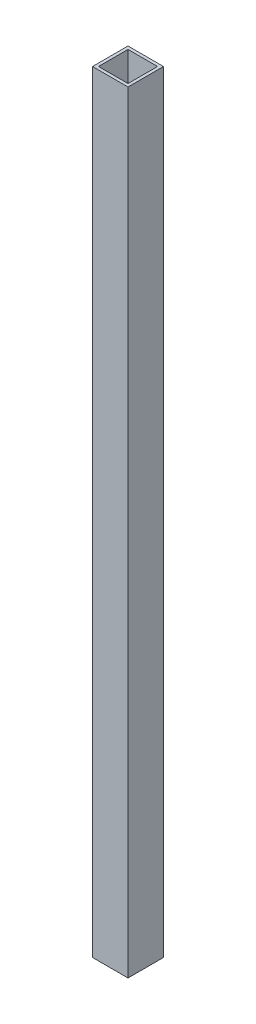
SolidWorks part; units mm, degrees
ref_plane "Front" through (0, 0, 0) normal (0, 0, 1) x (1, 0, 0)
ref_plane "Top" through (0, 0, 0) normal (0, 1, 0) x (1, 0, 0)
ref_plane "Right" through (0, 0, 0) normal (1, 0, 0) x (0, 0, -1)
sketch "Sketch2" plane through (0, 0, 0) normal (0, 1, 0) x (1, 0, 0)
  line L0 (1.5875, 1.5875) -> (17.4625, 1.5875)
  line L1 (0, 0) -> (19.05, 0)
  line L2 (0, 0) -> (0, 19.05)
  line L3 (0, 19.05) -> (19.05, 19.05)
  line L4 (19.05, 0) -> (19.05, 19.05)
  line L5 (17.4625, 1.5875) -> (17.4625, 17.4625)
  line L6 (1.5875, 17.4625) -> (17.4625, 17.4625)
  line L7 (1.5875, 1.5875) -> (1.5875, 17.4625)
extrude "Boss-Extrude1" add sketch "Sketch2" along normal blind 414.3375
